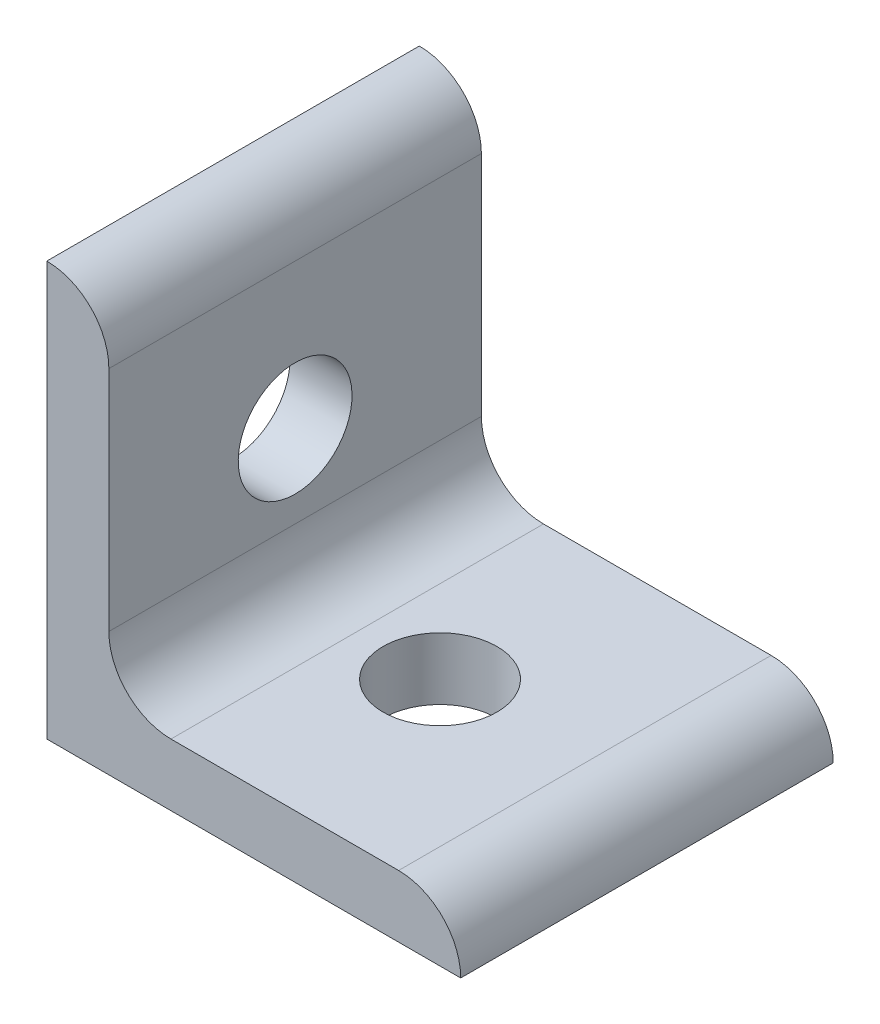
SolidWorks part; units mm, degrees
ref_plane "Front Plane" through (0, 0, 0) normal (0, 0, 1) x (1, 0, 0)
ref_plane "Top Plane" through (0, 0, 0) normal (0, 1, 0) x (1, 0, 0)
ref_plane "Right Plane" through (0, 0, 0) normal (1, 0, 0) x (0, 0, -1)
sketch "Sketch1" plane through (0, 0, 0) normal (0, 0, 1) x (1, 0, 0)
  line L0 (0, 0) -> (0, 20)
  line L1 (3, 17) -> (3, 20) construction
  line L2 (3, 17) -> (3, 6)
  line L3 (6, 3) -> (17, 3)
  line L4 (3, 20) -> (0, 20) construction
  line L5 (20, 0) -> (0, 0)
  line L6 (17, 3) -> (20, 3) construction
  line L7 (20, 3) -> (20, 0) construction
  arc A0 (3, 17) -> (0, 20) centre (0, 17) ccw
  arc A1 (20, 0) -> (17, 3) centre (17, 0) ccw
  arc A2 (3, 6) -> (6, 3) centre (6, 6) ccw
  point P10 (3, 18.5)
  dimension "E" = 3
  dimension "D" = 3
  dimension "C" = 20
  dimension "B" = 20
extrude "Boss-Extrude1" add sketch "Sketch1" along normal mid plane 18
sketch "Sketch2" plane through (0, 0, 0) normal (0, 1, 0) x (1, 0, 0)
  line L0 (0, 0) -> (10, 0) construction
  circle A0 centre (10, 0) radius 2.75
  dimension "D1" = 10
  dimension "E" = 5.5
extrude "Cut-Extrude1" cut sketch "Sketch2" along normal through all
sketch "Sketch3" plane through (0, 0, 0) normal (1, 0, 0) x (0, 0, -1)
  line L0 (0, 0) -> (0, 10) construction
  circle A0 centre (0, 10) radius 2.75
  dimension "D1" = 10
  dimension "E" = 5.5
extrude "Cut-Extrude2" cut sketch "Sketch3" along normal through all
equation "\"E@Sketch3\" = \"E@Sketch2\""
equation "\"D1@Sketch3\" = \"D1@Sketch2\""
